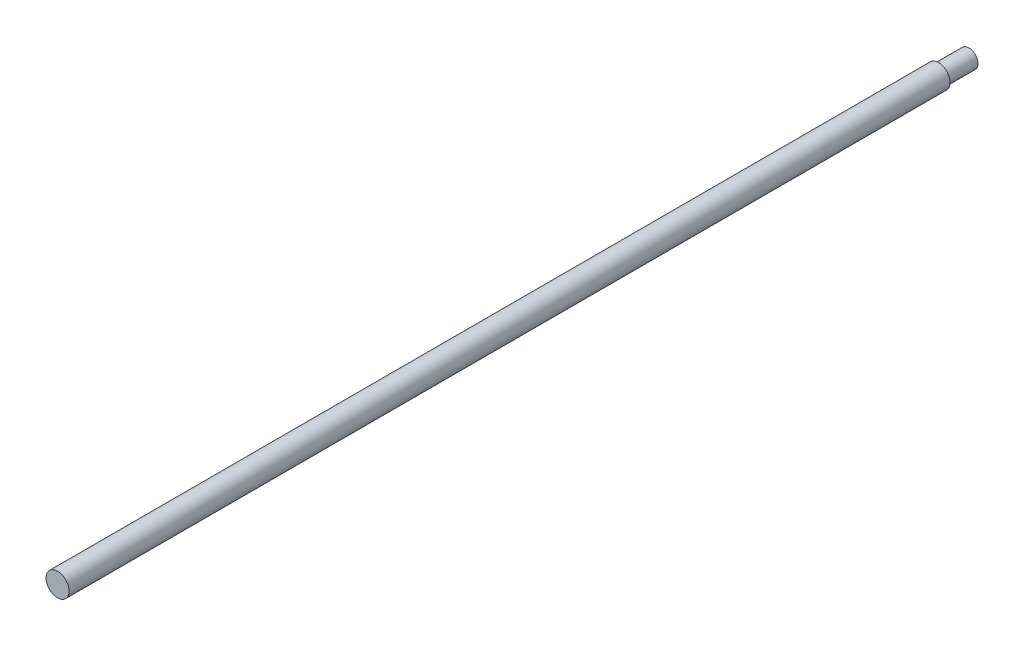
SolidWorks part; units mm, degrees
ref_plane "Front Plane" through (0, 0, 0) normal (0, 0, 1) x (1, 0, 0)
ref_plane "Top Plane" through (0, 0, 0) normal (0, 1, 0) x (1, 0, 0)
ref_plane "Right Plane" through (0, 0, 0) normal (1, 0, 0) x (0, 0, -1)
sketch "Sketch1" plane through (0, 0, 0) normal (0, 0, 1) x (1, 0, 0)
  circle A0 centre (0, 0) radius 3.8
  dimension "D1" = 7.6
extrude "Boss-Extrude1" add sketch "Sketch1" along normal blind 300
sketch "Sketch2" plane through (0, 0, 0) normal (0, 0, -1) x (-1, 0, 0)
  circle A0 centre (0, 0) radius 3
  dimension "D1" = 6
extrude "Cut-Extrude1" cut sketch "Sketch2" against normal blind 10 flip side to cut
